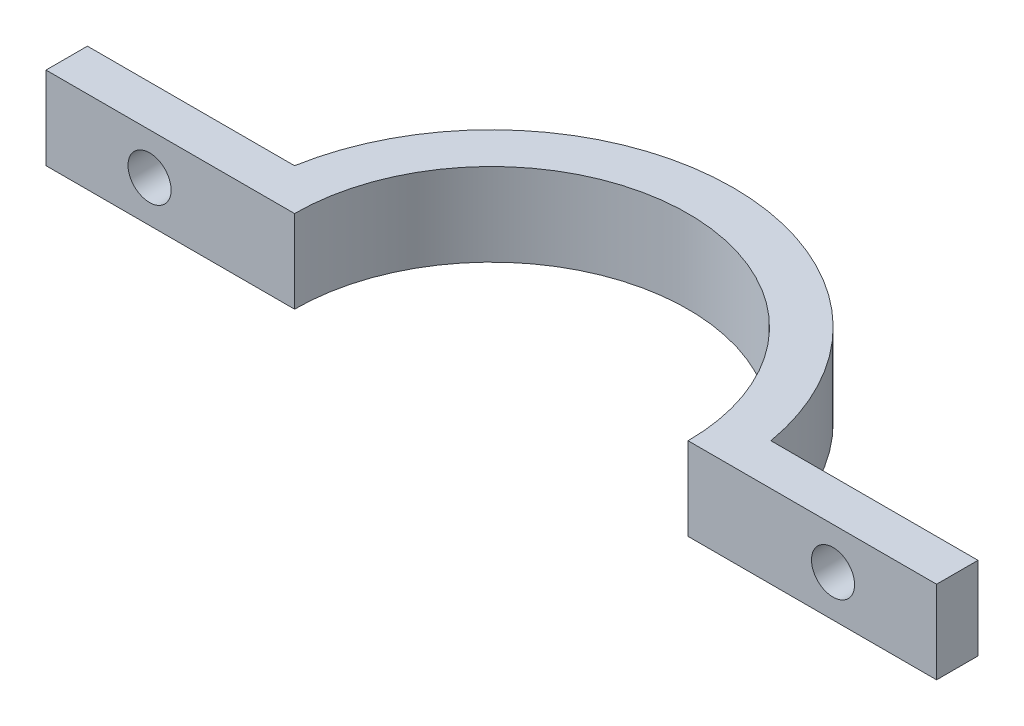
SolidWorks part; units mm, degrees
ref_plane "Front Plane" through (0, 0, 0) normal (0, 0, 1) x (1, 0, 0)
ref_plane "Top Plane" through (0, 0, 0) normal (0, 1, 0) x (1, 0, 0)
ref_plane "Right Plane" through (0, 0, 0) normal (1, 0, 0) x (0, 0, -1)
sketch "Sketch1" plane through (0, 0, 0) normal (0, 1, 0) x (1, 0, 0)
  line L0 (-15.0813, 0) -> (-34.1313, 0)
  line L1 (-34.1313, 0) -> (-34.1313, 3.175)
  line L2 (-34.1313, 3.175) -> (-18.2563, 3.175)
  line L3 (0, 0.5186) -> (0, 27.6562) construction
  line L4 (34.1313, 3.175) -> (18.2563, 3.175)
  line L5 (34.1313, 0) -> (34.1313, 3.175)
  line L6 (15.0813, 0) -> (34.1313, 0)
  arc A0 (-15.0813, 0) -> (15.0813, 0) centre (0, 0) cw
  arc A1 (-18.2563, 3.175) -> (18.2563, 3.175) centre (0, 0) cw
  dimension "D1" = 15.0813
  dimension "D2" = 19.05
  dimension "D3" = 3.175
  dimension "D4" = 15.875
extrude "Boss-Extrude1" add sketch "Sketch1" along normal blind 6.35
sketch "Sketch2" plane through (0, 0, -3.175) normal (0, 0, -1) x (-1, 0, 0)
  line L0 (18.2563, 3.175) -> (34.1313, 3.175) construction
  line L1 (18.2563, 6.35) -> (18.2563, 0) construction
  line L2 (34.1313, 6.35) -> (34.1313, 0) construction
  circle A0 centre (26.1938, 3.175) radius 1.651
  dimension "D1" = 3.302
extrude "Cut-Extrude1" cut sketch "Sketch2" against normal blind 6.35
mirror "Mirror1" about plane through (0, 0, 0) normal (1, 0, 0) of "Cut-Extrude1"
